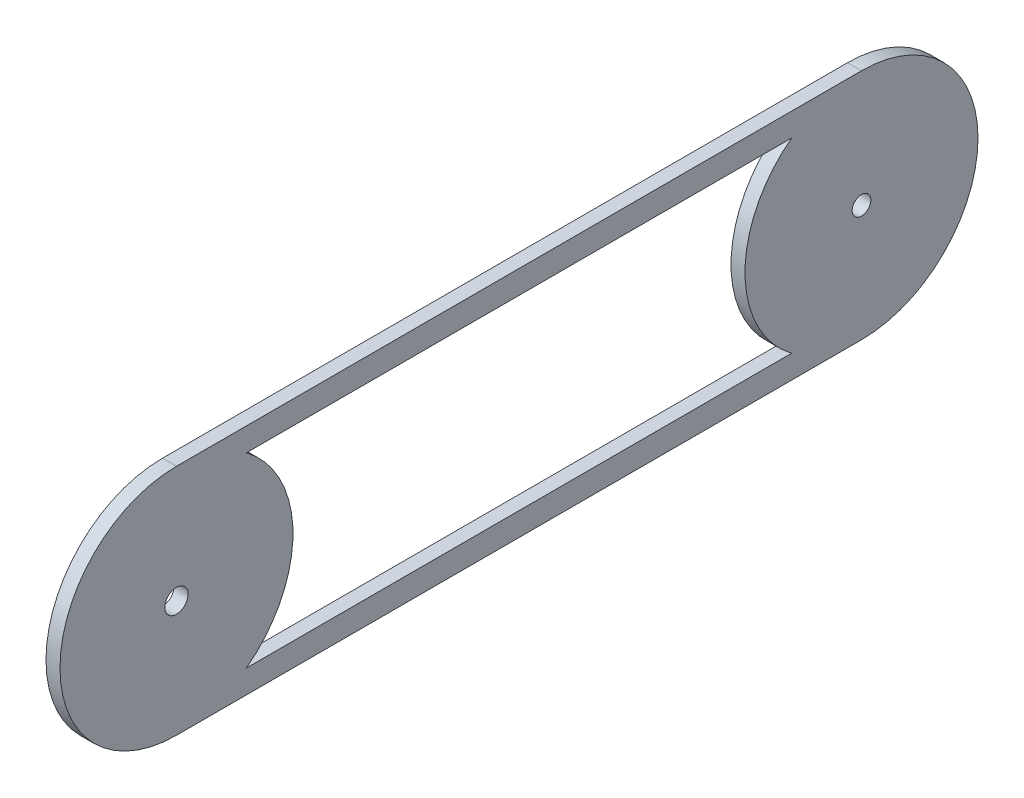
SolidWorks part; units mm, degrees
ref_plane "Front Plane" through (0, 0, 0) normal (0, 0, 1) x (1, 0, 0)
ref_plane "Top Plane" through (0, 0, 0) normal (0, 1, 0) x (1, 0, 0)
ref_plane "Right Plane" through (0, 0, 0) normal (1, 0, 0) x (0, 0, -1)
sketch "Sketch1" plane through (0, 0, 0) normal (1, 0, 0) x (0, 0, -1)
  line L0 (0, 25) -> (-147, 25)
  line L1 (0, -25) -> (-147, -25)
  line L2 (0, 20) -> (-147, 20)
  line L3 (0, -20) -> (-147, -20)
  arc A1 (0, 25) -> (0, -25) centre (0, 0) cw
  arc A2 (-147, 25) -> (-147, -25) centre (-147, 0) ccw
  arc A3 (-147, 20) -> (-147, -20) centre (-147, 0) ccw
  arc A4 (0, 20) -> (0, -20) centre (0, 0) cw
  circle A5 centre (-147, 0) radius 25
  circle A6 centre (0, 0) radius 25
  circle A7 centre (-147, 0) radius 2.5
  circle A8 centre (0, 0) radius 2
  dimension "D1" = 25
  dimension "D5" = 5
  dimension "D4" = 4
  dimension "D2" = 147
  dimension "D3" = 5
extrude "Boss-Extrude1" add sketch "Sketch1" along normal blind 3 contours L2 A5 A2 L3 A3 | L3 A5 L2 A3 | A6 L0 A5 L2 | A1 A6 L2 A4 L3 | L2 A6 L3 A4 | A6 L3 A5 L1
